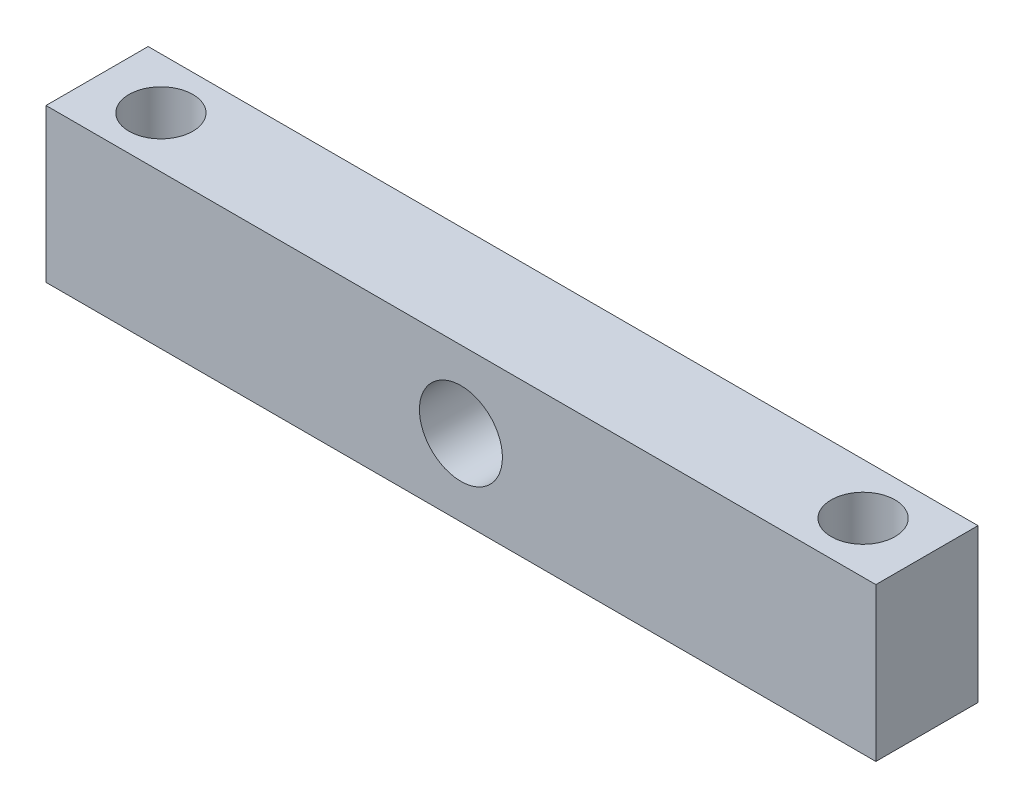
SolidWorks part; units mm, degrees
material "Plain Carbon Steel"
ref_plane "Front Plane" through (0, 0, 0) normal (0, 0, 1) x (1, 0, 0)
ref_plane "Top Plane" through (0, 0, 0) normal (0, 1, 0) x (1, 0, 0)
ref_plane "Right Plane" through (0, 0, 0) normal (1, 0, 0) x (0, 0, -1)
sketch "Sketch2" plane through (0, 0, 0) normal (0, 1, 0) x (1, 0, 0)
  line L0 (-27.5, 0) -> (27.5, 0) construction
  line L5 (-32.5, -4) -> (32.5, -4)
  line L6 (-32.5, -4) -> (-32.5, 4)
  line L7 (-32.5, 4) -> (32.5, 4)
  line L8 (32.5, -4) -> (32.5, 4)
  line L9 (-32.5, -4) -> (32.5, 4) construction
  line L10 (-32.5, 4) -> (32.5, -4) construction
  circle A0 centre (-27.5, 0) radius 2.5
  circle A1 centre (27.5, 0) radius 2.5
  point P0 (0, 0)
  point P10 (0, 0)
  dimension "D4" = 5
  dimension "D1" = 8
  dimension "D2" = 65
  dimension "D3" = 55
extrude "Boss-Extrude1" add sketch "Sketch2" along normal blind 12
sketch "Sketch3" plane through (0, 0, 4) normal (0, 0, 1) x (1, 0, 0)
  line L0 (32.5, 12) -> (32.5, 0) construction
  circle A0 centre (0, 6) radius 3.25
  point P7 (32.5, 6)
  dimension "D1" = 6.5
extrude "Cut-Extrude1" cut sketch "Sketch3" against normal through all
